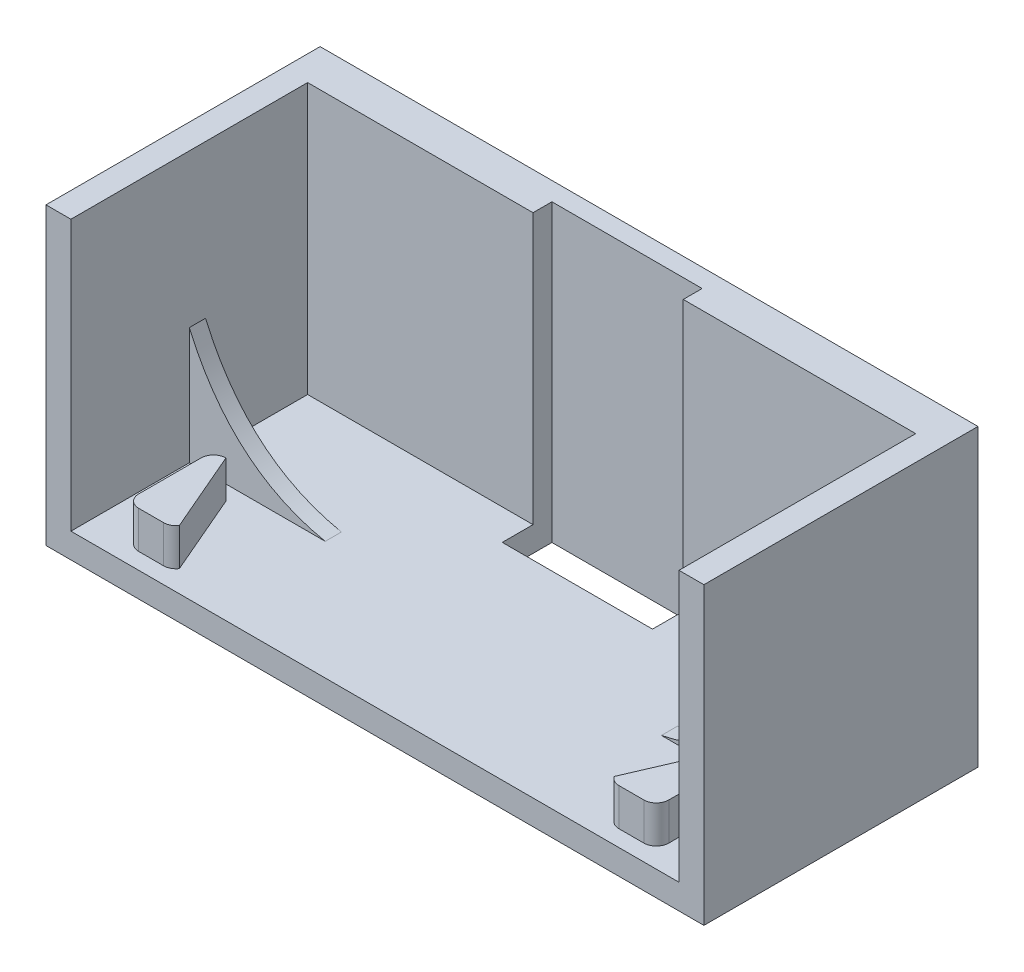
SolidWorks part; units mm, degrees
ref_plane "Alzado" through (0, 0, 0) normal (0, 0, 1) x (1, 0, 0)
ref_plane "Planta" through (0, 0, 0) normal (0, 1, 0) x (1, 0, 0)
ref_plane "Vista lateral" through (0, 0, 0) normal (1, 0, 0) x (0, 0, -1)
sketch "Croquis1" plane through (0, 0, 0) normal (0, 0, 1) x (1, 0, 0)
  line L6 (-24.404, 20.4) -> (-24.404, -1.2848)
  line L7 (-24.404, -1.2848) -> (24.404, -1.2848)
  line L8 (24.404, -1.2848) -> (24.404, 20.4)
  line L9 (-26.404, 20.4) -> (-26.404, -3.2848)
  line L10 (-26.404, -3.2848) -> (26.404, -3.2848)
  line L11 (26.404, -3.2848) -> (26.404, 20.4)
  line L12 (-26.404, 20.4) -> (-26.404, -3.2848)
  line L13 (-26.404, -3.2848) -> (26.404, -3.2848)
  line L14 (26.404, -3.2848) -> (26.404, 20.4)
  line L15 (26.404, 20.4) -> (24.404, 20.4)
  line L16 (-26.404, 20.4) -> (-24.404, 20.4)
  dimension "D1" = 2
  dimension "D2" = 2
extrude "Saliente-Extruir1" add sketch "Croquis1" against normal blind 19
sketch "Croquis3" plane through (0, 0, -19) normal (0, 0, -1) x (-1, 0, 0)
  line L1 (-26.404, -3.2848) -> (26.404, -3.2848)
  line L2 (-26.404, -3.2848) -> (-26.404, 20.4)
  line L3 (-26.404, 20.4) -> (26.404, 20.4)
  line L4 (26.404, -3.2848) -> (26.404, 20.4)
extrude "Saliente-Extruir2" add sketch "Croquis3" along normal blind 3
sketch "Croquis4" plane through (0, -3.2848, 0) normal (0, -1, 0) x (1, 0, 0)
  line L1 (5.745, -16.5331) -> (-6.3129, -16.5331)
  line L2 (5.745, -16.5331) -> (5.745, -20.5175)
  line L3 (5.745, -20.5175) -> (-6.3129, -20.5175)
  line L4 (-6.3129, -16.5331) -> (-6.3129, -20.5175)
extrude "Cortar-Extruir1" cut sketch "Croquis4" against normal blind 26
ref_plane "Plano1" through (0, 0, 0) normal (-1, 0, 0) x (0, 0, 1)
sketch "Croquis8" plane through (0, -1.2848, 0) normal (0, 1, 0) x (1, 0, 0)
  line L0 (-20.2732, 7.3116) -> (-20.2732, 2.3116) construction
  line L1 (-19.2732, 7.3116) -> (-19.2732, 2.3116) construction
  line L2 (-21.2732, 7.3116) -> (-21.2732, 2.3116) construction
  line L3 (0, 5.1412) -> (0, 0) construction
  line L4 (20.2732, 7.3116) -> (20.2732, 2.3116) construction
  line L5 (19.2732, 7.3116) -> (19.2732, 2.3116) construction
  line L6 (21.2732, 7.3116) -> (21.2732, 2.3116) construction
  line L7 (-20.2732, 4.8116) -> (-18.2732, 4.8116) construction
  line L8 (-20.2732, 2.3116) -> (-18.2732, 4.8116) construction
  line L9 (-20.2732, 5.8116) -> (-18.2732, 5.8116) construction
  line L10 (-20.2732, 3.8116) -> (-18.2732, 3.8116) construction
  line L11 (20.2732, 4.8116) -> (18.2732, 4.8116) construction
  line L12 (20.2732, 5.8116) -> (18.2732, 5.8116) construction
  line L13 (20.2732, 3.8116) -> (18.2732, 3.8116) construction
  line L14 (-21.2732, 8.3116) -> (-17.2732, 8.3116) construction
  line L15 (-21.2732, 8.3116) -> (-21.2732, 1.3116) construction
  line L16 (-21.2732, 1.3116) -> (-17.2732, 1.3116) construction
  line L17 (-17.2732, 8.3116) -> (-17.2732, 1.3116) construction
  line L18 (-18.2732, 4.8116) -> (-18.2732, 2.3116) construction
  line L19 (-18.2732, 2.3116) -> (-20.2732, 2.3116) construction
  line L20 (-20.2732, 1.3116) -> (-18.2732, 1.3116)
  line L21 (-20.2732, 8.3116) -> (-17.4472, 1.7479)
  line L22 (-21.2732, 7.3116) -> (-21.2732, 2.3116)
  line L23 (20.2732, 1.3116) -> (18.2732, 1.3116)
  line L24 (20.2732, 8.3116) -> (17.4472, 1.7479)
  line L25 (21.2732, 7.3116) -> (21.2732, 2.3116)
  arc A0 (-20.2732, 8.3116) -> (-21.2732, 7.3116) centre (-20.2732, 7.3116) ccw construction
  arc A1 (-21.2732, 2.3116) -> (-20.2732, 1.3116) centre (-20.2732, 2.3116) ccw construction
  arc A2 (19.2732, 7.3116) -> (21.2732, 7.3116) centre (20.2732, 7.3116) cw construction
  arc A3 (21.2732, 2.3116) -> (19.2732, 2.3116) centre (20.2732, 2.3116) cw construction
  arc A4 (-20.2732, 5.8116) -> (-20.2732, 3.8116) centre (-20.2732, 4.8116) ccw construction
  arc A5 (-18.2732, 3.8116) -> (-18.2732, 5.8116) centre (-18.2732, 4.8116) ccw construction
  arc A6 (20.2732, 5.8116) -> (20.2732, 3.8116) centre (20.2732, 4.8116) cw construction
  arc A7 (18.2732, 3.8116) -> (18.2732, 5.8116) centre (18.2732, 4.8116) cw construction
  arc A8 (-20.2732, 8.3116) -> (-21.2732, 7.3116) centre (-20.2732, 7.3116) ccw
  arc A9 (-21.2732, 2.3116) -> (-20.2732, 1.3116) centre (-20.2732, 2.3116) ccw
  arc A10 (-18.2732, 1.3116) -> (-17.4472, 1.7479) centre (-18.2732, 2.3116) ccw
  arc A11 (18.2732, 1.3116) -> (17.4472, 1.7479) centre (18.2732, 2.3116) cw
  arc A12 (21.2732, 2.3116) -> (20.2732, 1.3116) centre (20.2732, 2.3116) cw
  arc A13 (20.2732, 8.3116) -> (21.2732, 7.3116) centre (20.2732, 7.3116) cw
  point P2 (-20.2732, 4.8116)
  point P13 (20.2732, 4.8116)
  point P22 (-19.2732, 4.8116)
  point P29 (19.2732, 4.8116)
extrude "Saliente-Extruir3" add sketch "Croquis8" along normal blind 3 contours A4 L9 L1 A0 L2 | L9 A4 L10 L1 | A4 L2 A1 L1 L10 | L10 A5 L9 L1 | A7 L13 L5 L12 | L6 A6 L13 L5 A3 | L12 A6 L6 A2 L5 | A6 L12 L5 L13 | L20 A10 L21 A8 L22 A9 | A13 L24 A11 L23 A12 L25
ref_plane "Plano2" through (0, 0, -9.5) normal (0, 0, -1) x (-1, 0, 0)
sketch "Croquis9" plane through (0, 0, -9.5) normal (0, 0, -1) x (-1, 0, 0)
  line L0 (0, -3.2848) -> (0, 26.6672) construction
  line L3 (24.404, -1.2848) -> (13.4912, -1.2848)
  line L4 (-24.404, -1.2848) -> (24.404, -1.2848) construction
  line L5 (24.404, -1.2848) -> (24.404, 8.115)
  line L6 (24.404, -1.2848) -> (24.404, 20.4) construction
  line L7 (24.404, 8.115) -> (20.955, 0.2152) construction
  line L13 (20.955, 0.2152) -> (13.4912, -1.2848) construction
  line L15 (26.404, -3.2848) -> (-26.404, -3.2848) construction
  line L16 (-24.404, -1.2848) -> (-13.4912, -1.2848)
  line L17 (-24.404, -1.2848) -> (-24.404, 8.115)
  line L18 (-24.404, 8.115) -> (-20.955, 0.2152) construction
  line L19 (-20.955, 0.2152) -> (-13.4912, -1.2848) construction
  spline S0 degree 2 poles (24.404, 8.115) (20.955, 0.2152) (13.4912, -1.2848) knots 0 0 0 1 1 1
  spline S1 degree 2 poles (-24.404, 8.115) (-20.955, 0.2152) (-13.4912, -1.2848) knots 0 0 0 1 1 1
extrude "Saliente-Extruir4" add sketch "Croquis9" along normal blind 1.3
